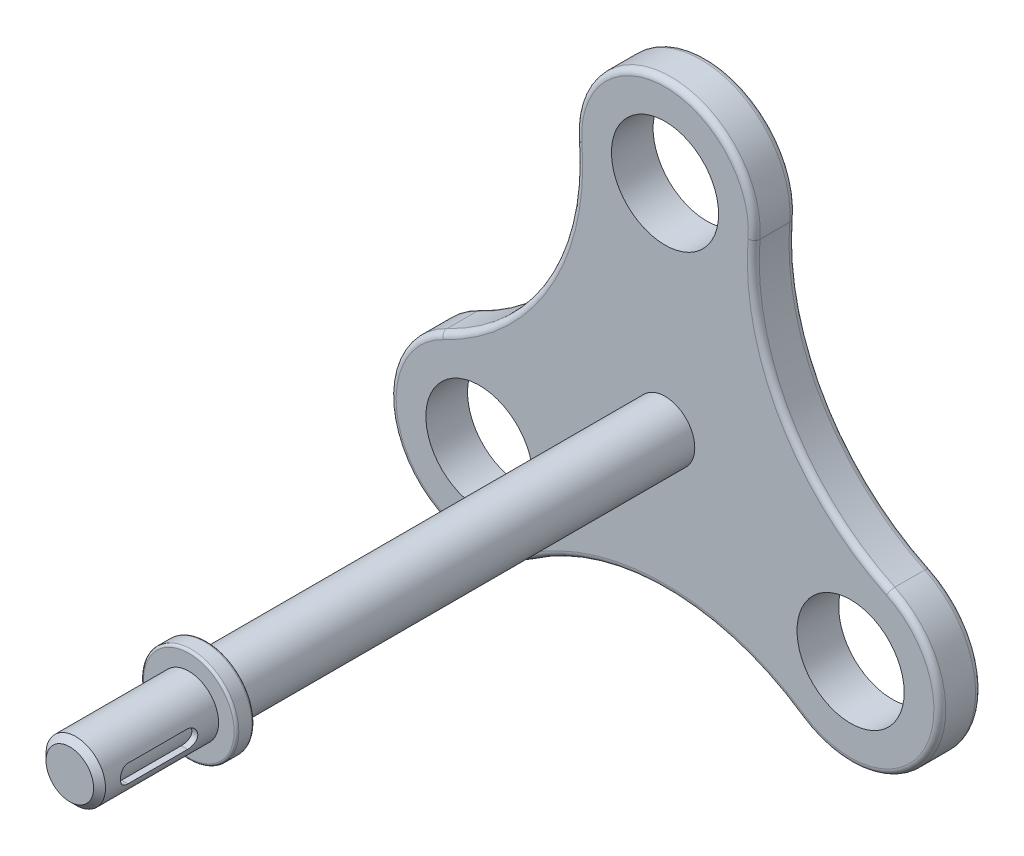
SolidWorks part; units mm, degrees
material "AISI 1020"
ref_plane "Front Plane" through (0, 0, 0) normal (0, 0, 1) x (1, 0, 0)
ref_plane "Top Plane" through (0, 0, 0) normal (0, 1, 0) x (1, 0, 0)
ref_plane "Right Plane" through (0, 0, 0) normal (1, 0, 0) x (0, 0, -1)
sketch "Sketch1" plane through (0, 0, 0) normal (0, 0, 1) x (1, 0, 0)
  circle A0 centre (0, 18) radius 4.5
  circle A1 centre (0, 18) radius 7.5
  circle A2 centre (15.5885, -9) radius 4.5
  circle A3 centre (15.5885, -9) radius 7.5
  circle A4 centre (-15.5885, -9) radius 4.5
  circle A5 centre (-15.5885, -9) radius 7.5
  arc A6 (7.4766, 17.4075) -> (18.8136, -2.2289) centre (27.4141, 15.8275) ccw
  arc A7 (11.3371, -15.1786) -> (-11.3371, -15.1786) centre (0, -31.655) ccw
  arc A8 (-18.8136, -2.2289) -> (-7.4766, 17.4075) centre (-27.4141, 15.8275) ccw
  point P12 (0, 0)
  point P14 (0, 0)
  point P15 (-18.8136, -2.2289)
  point P16 (-18.8136, -2.2289)
  dimension "D1" = 9
  dimension "D2" = 15
  dimension "D5" = 20
  dimension "D3" = 18
  dimension "D4" = 3
  dimension "D6" = 3
extrude "Boss-Extrude1" add sketch "Sketch1" along normal blind 3.5 contours A1 A0 | A5 A4 | A3 A2 | A8 A5 A7 A3 A6 A1
sketch "Sketch3" plane through (0, 0, 3.5) normal (0, 0, 1) x (1, 0, 0)
  circle A0 centre (0, 0) radius 2.5
extrude "Boss-Extrude2" add sketch "Sketch3" along normal blind 50
sketch "Sketch4" plane through (0, 0, 53.5) normal (0, 0, 1) x (1, 0, 0)
  circle A0 centre (0, 0) radius 4
extrude "Boss-Extrude3" add sketch "Sketch4" against normal blind 1.5 from offset 10 offset against normal yes
sketch "Sketch6" plane through (0, 0, 0) normal (1, 0, 0) x (0, 0, -1)
  line L0 (-46, 0) -> (-51, 0) construction
  line L1 (-46, -0.75) -> (-51, -0.75)
  line L2 (-46, 0.75) -> (-51, 0.75)
  line L3 (-53.5, 2.5) -> (-53.5, -2.5) construction
  arc A0 (-46, -0.75) -> (-46, 0.75) centre (-46, 0) ccw
  arc A1 (-51, 0.75) -> (-51, -0.75) centre (-51, 0) ccw
  point P2 (-48.5, 0)
  dimension "D1" = 5
  dimension "D2" = 5
  dimension "D3" = 1.5
extrude "Cut-Extrude1" cut sketch "Sketch6" against normal offset from surface (3.146 mm away) 0.5 from offset 5
chamfer "Chamfer1" distance 0.5 angle 45 1 edges at (2.5, 0, 53.5)
fillet "Fillet1" radius 0.2 2 edges at (4, 0, 43.5) (4, 0, 42)
fillet "Fillet2" radius 0.5 12 edges at (0, 25.5, 0) (0, 25.5, 3.5) (-10.0935, 5.8275, 0) (-10.0935, 5.8275, 3.5) (-22.0836, -12.75, 0) (-22.0836, -12.75, 3.5) (0, -11.655, 0) (0, -11.655, 3.5) (22.0836, -12.75, 0) (22.0836, -12.75, 3.5) (10.0935, 5.8275, 0) (10.0935, 5.8275, 3.5)
